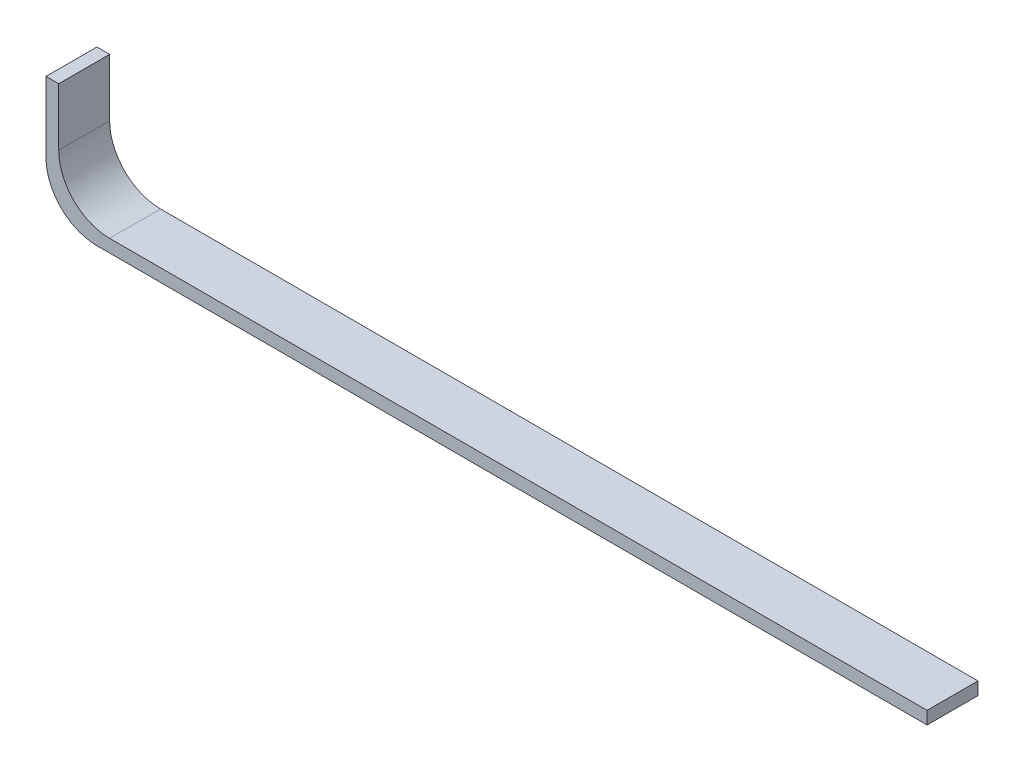
SolidWorks part; units mm, degrees
ref_plane "Front Plane" through (0, 0, 0) normal (0, 0, 1) x (1, 0, 0)
ref_plane "Top Plane" through (0, 0, 0) normal (0, 1, 0) x (1, 0, 0)
ref_plane "Right Plane" through (0, 0, 0) normal (1, 0, 0) x (0, 0, -1)
sketch "Sketch1" plane through (0, 0, 0) normal (0, 0, 1) x (1, 0, 0)
  line L0 (0, 0) -> (0, -3.507)
  line L1 (2.54, -6.047) -> (43.9665, -6.047)
  line L2 (0, 0) -> (0.635, 0)
  line L3 (0.635, 0) -> (0.635, -2.872)
  line L4 (3.175, -5.412) -> (43.9665, -5.412)
  line L5 (43.9665, -5.412) -> (43.9665, -6.047)
  arc A0 (0, -3.507) -> (2.54, -6.047) centre (2.54, -3.507) ccw
  arc A1 (0.635, -2.872) -> (3.175, -5.412) centre (3.175, -2.872) ccw
  dimension "D3" = 2.54
  dimension "D1" = 0.635
  dimension "D2" = 0.635
extrude "Extrude1" add sketch "Sketch1" along normal blind 2.54
